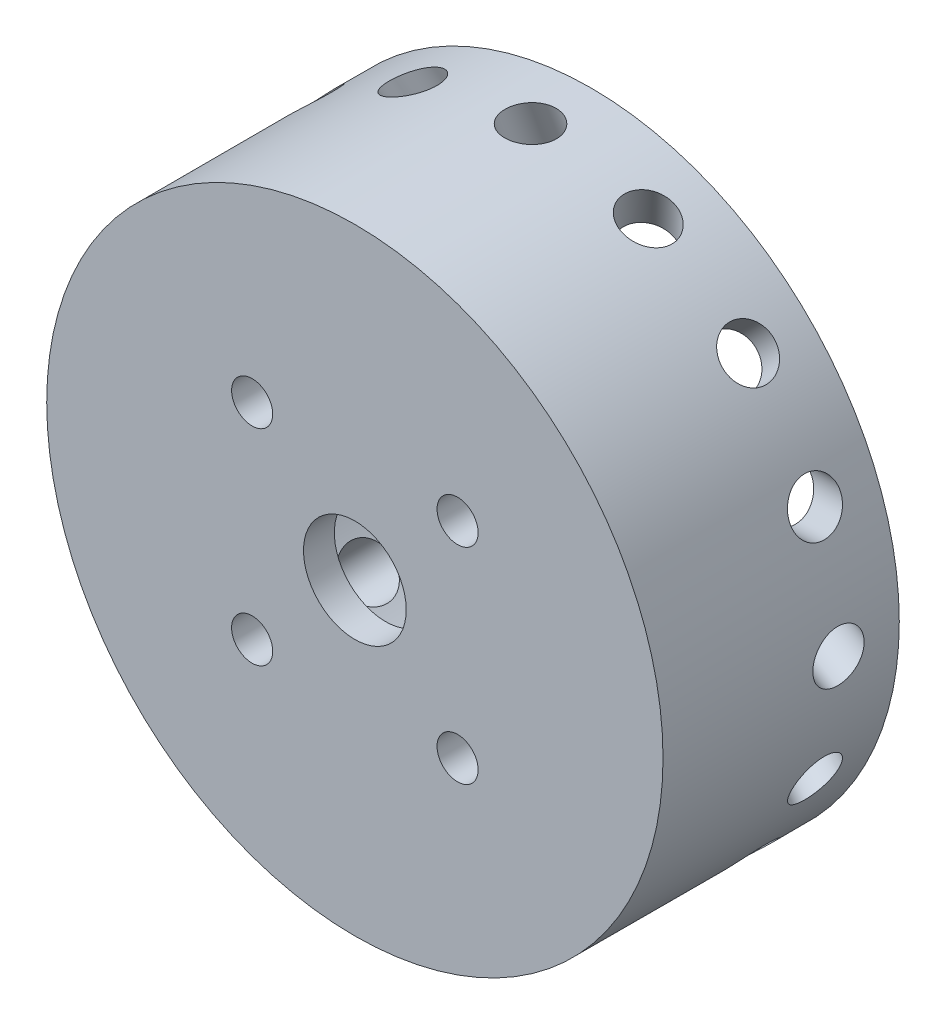
SolidWorks part; units mm, degrees
ref_plane "Plan de face" through (0, 0, 0) normal (0, 0, 1) x (1, 0, 0)
ref_plane "Plan de dessus" through (0, 0, 0) normal (0, 1, 0) x (1, 0, 0)
ref_plane "Plan de droite" through (0, 0, 0) normal (1, 0, 0) x (0, 0, -1)
sketch "Esquisse1" plane through (0, 0, 0) normal (0, 0, 1) x (1, 0, 0)
  circle A0 centre (0, 0) radius 30
  circle A1 centre (0, 0) radius 25
  dimension "D1" = 60
  dimension "D2" = 50
extrude "Boss.-Extru.1" add sketch "Esquisse1" along normal blind 20
sketch "Esquisse2" plane through (0, 0, 20) normal (0, 0, 1) x (1, 0, 0)
  circle A0 centre (0, 0) radius 30
extrude "Boss.-Extru.2" add sketch "Esquisse2" along normal blind 3
sketch "Esquisse4" plane through (0, 0, 23) normal (0, 0, 1) x (1, 0, 0)
  line L0 (0, 0) -> (0, 26.3953) construction
  line L1 (0, 0) -> (27.5582, 0) construction
  circle A0 centre (10, 10) radius 2
  dimension "D1" = 4
  dimension "D2" = 10
  dimension "D3" = 10
extrude "Enlèv. mat.-Extru.1" cut sketch "Esquisse4" against normal through all
pattern_circular "Répétition circulaire1" count 4 every 90 about axis through (0, 0, 0) along (0, 0, 1) of "Enlèv. mat.-Extru.1"
sketch "Esquisse5" plane through (0, 0, 0) normal (0, 1, 0) x (1, 0, 0)
  line L0 (0, -23) -> (0, 0) construction
  line L1 (30, 0) -> (-30, 0) construction
  circle A0 centre (0, 5) radius 2.5
  dimension "D1" = 5
  dimension "D2" = 0
  dimension "D3" = 5
sketch "Esquisse6" plane through (0, 0, 0) normal (1, 0, 0) x (0, 0, -1)
  line L0 (4.9191, 0) -> (-23, 0) construction
  line L1 (-23, 0) -> (0, 0) construction
  line L2 (4.9191, 0) -> (-6, -30)
  line L3 (-23, -30) -> (0, -30) construction
  line L4 (0, -30) -> (0, 30) construction
  dimension "D1" = 70
  dimension "D2" = 0
  dimension "D3" = 6
sweep "Enlèvement de matière-Balayage1" cut profiles "Esquisse5" path "Esquisse6"
pattern_circular "Répétition circulaire2" count 16 over 360 about axis through (0, 0, 20) along (0, 0, -1) of "Enlèvement de matière-Balayage1"
sketch "Esquisse7" plane through (0, 0, 23) normal (0, 0, 1) x (1, 0, 0)
  circle A0 centre (0, 0) radius 5
  dimension "D1" = 10
extrude "Enlèv. mat.-Extru.2" cut sketch "Esquisse7" against normal through all
